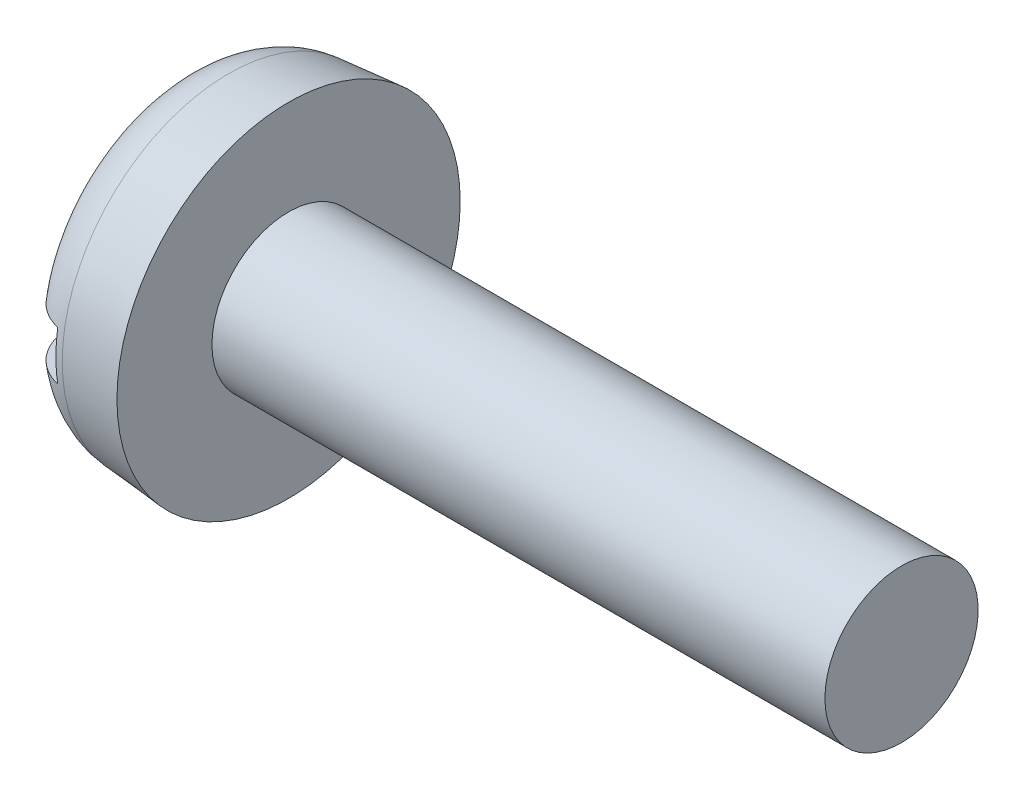
SolidWorks part; units mm, degrees
ref_plane "Plane1" through (0, 0, 0) normal (0, 0, 1) x (1, 0, 0)
ref_plane "Plane2" through (0, 0, 0) normal (0, 1, 0) x (1, 0, 0)
ref_plane "Plane3" through (0, 0, 0) normal (1, 0, 0) x (0, 0, -1)
sketch "BodySke" plane through (0, 0, 0) normal (0, 0, 1) x (1, 0, 0)
  line L0 (1.8, 1.25) -> (1.8, 2.8)
  line L1 (0, 0) -> (0, 2.6425)
  line L2 (-25.4, 0) -> (127, 0) construction
  line L3 (11.8, 0) -> (0, 0)
  line L4 (1.8, 1.25) -> (11.8, 1.25)
  line L5 (11.8, 1.25) -> (11.8, 0)
  line L6 (0, 2.6425) -> (1.8, 2.8)
  line L9 (2.3, 2.8375) -> (2.3, -6.6875) construction
  line L10 (1.8, 6.35) -> (1.8, -3.175) construction
  dimension "Head_ht" = 1.8
  dimension "Diameter" = 2.5
  dimension "Length" = 10
  dimension "Head_dia" = 5.6
  dimension "Advance" = 0.5
  dimension "Thread_nom" = 10
  dimension "Head_side_angle" = 5
revolve "Base-Revolve" add sketch "BodySke"
cosmetic thread "ThreadCosmetic"
fillet "Fillet1" [suppressed] radius 0.1
fillet "Fillet2" radius 0.9 1 edges at (0, 0, 2.6425)
sketch "Sketch2" plane through (0, 0, 0) normal (1, 0, 0) x (0, 0, -1)
  line L0 (2.8, -0.4) -> (-2.8, -0.4)
  line L1 (2.8, -0.4) -> (2.8, 0.4)
  line L2 (-2.8, 0.4) -> (2.8, 0.4)
  line L3 (-2.8, 0.4) -> (-2.8, -0.4)
  dimension "D1" = 5.6
  dimension "D2" = 2.8
  dimension "Slot_width" = 0.8
  dimension "D3" = 0.4
extrude "Slot" cut sketch "Sketch2" along normal blind 0.7
sketch "ThdSchSke" plane through (0, 0, 0) normal (0, 0, 1) x (1, 0, 0)
  line L0 (2.8, -1.2195) -> (2.7786, -1.25)
  line L1 (2.8, -1.2195) -> (2.8214, -1.25)
  line L2 (2.8214, -1.25) -> (2.8214, -1.5625)
  line L3 (-3.175, 0) -> (5.1513, 0) construction
  line L5 (2.8214, -1.5625) -> (2.7786, -1.5625)
  line L6 (2.7786, -1.5625) -> (2.7786, -1.25)
  dimension "Thread_minor" = 2.439
  dimension "Diameter" = 2.5
  dimension "Start" = 2.8
  dimension "SideAngle" = 55
  dimension "VeeAngle" = 70
  dimension "Overcut" = 3.125
revolve "ThreadSchematic" [suppressed] cut sketch "ThdSchSke" angle 360 about L3
pattern_linear "ThdSchPat" [suppressed]
equation "\"D1@Sketch2\" = \"Head_dia@BodySke\""
equation "\"D2@Sketch2\" = \"D1@Sketch2\" / 2"
equation "\"D3@Sketch2\" = \"Slot_width@Sketch2\" / 2"
equation "\"Thread_length@ThreadCosmetic\" = ((sgn( (\"Length@BodySke\" - \"Advance@BodySke\" * 2.0 ) - \"Thread_nom@BodySke\" )-1)*( (\"Length@BodySke\" - \"Advance@BodySke\"  * 2.0) - \"Thread_nom@BodySke\" ))/-2+ \"Thread_nom@BodySke\""
equation "\"Thread_minor@ThdSchSke\" = \"Thread_minor@ThreadCosmetic\""
equation "\"Diameter@ThdSchSke\" = \"Diameter@BodySke\""
equation "\"Overcut@ThdSchSke\" = \"Diameter@BodySke\" * 1.25"
equation "\"Start@ThdSchSke\" = \"Head_ht@BodySke\" + \"Length@BodySke\" - \"Thread_length@ThreadCosmetic\"  '---Non-countersunk---"
equation "\"Num_threads@ThdSchPat\" = int( \"Thread_length@ThreadCosmetic\" / \"Advance@BodySke\" + 0.999 )  + 1"
equation "\"Advance@ThdSchPat\" = \"Thread_length@ThreadCosmetic\" /  (\"Num_threads@ThdSchPat\" - 1) 'relax it"
